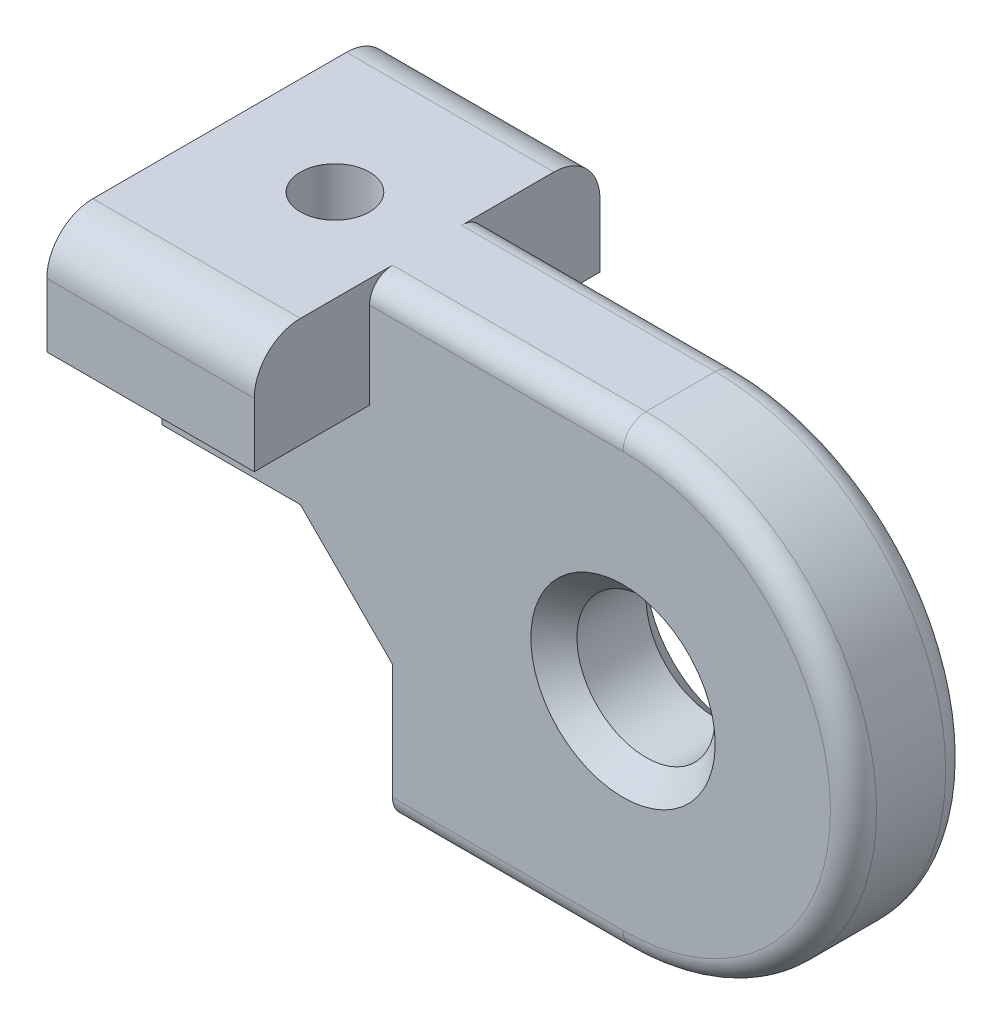
SolidWorks part; units mm, degrees
ref_plane "Front Plane" through (0, 0, 0) normal (0, 0, 1) x (1, 0, 0)
ref_plane "Top Plane" through (0, 0, 0) normal (0, 1, 0) x (1, 0, 0)
ref_plane "Right Plane" through (0, 0, 0) normal (1, 0, 0) x (0, 0, -1)
sketch "Sketch1" plane through (0, 0, 0) normal (0, 0, 1) x (1, 0, 0)
  line L0 (0, 10) -> (-20, 10)
  line L1 (-20, 10) -> (-20, 0)
  line L2 (-10, -10) -> (0, -10)
  line L3 (-20, 0) -> (-14, 0)
  line L4 (55, 0) -> (-55, 0) construction
  line L5 (-10, -4) -> (-10, -10)
  line L6 (-14, 0) -> (-10, -4)
  arc A0 (0, -10) -> (0, 10) centre (0, 0) ccw
  circle A1 centre (0, 0) radius 3
  point P6 (-10, 0)
  dimension "D1" = 20
  dimension "D2" = 6
  dimension "D3" = 20
  dimension "D4" = 10
extrude "Boss-Extrude1" add sketch "Sketch1" along normal mid plane 5
sketch "Sketch2" plane through (0, 0, 0) normal (0, 0, 1) x (1, 0, 0)
  line L0 (-20, 10) -> (-20, 5.2381)
  line L1 (-11, 5.2381) -> (-11, 10)
  line L2 (-11, 10) -> (-20, 10)
  line L5 (-20, 5.2381) -> (-11, 5.2381)
  dimension "D1" = 9
  dimension "D2" = 4.7619
extrude "Boss-Extrude2" add sketch "Sketch2" along normal mid plane 15
fillet "Fillet1" radius 2 2 edges at (-15.5, 10, -7.5) (-15.5, 10, 7.5)
chamfer "Chamfer1" distance 1 angle 45 2 edges at (3, 0, -2.5) (3, 0, 2.5)
fillet "Fillet2" radius 1 6 edges at (-5, -10, -2.5) (-5.5, 10, -2.5) (-5, -10, 2.5) (-5.5, 10, 2.5) (10, 0, -2.5) (10, 0, 2.5)
sketch "Sketch3" plane through (0, 10, 0) normal (0, 1, 0) x (1, 0, 0)
  line L0 (-11, 0) -> (11, 0) construction
  line L1 (-20, -5.5) -> (-20, 5.5) construction
  circle A0 centre (-15, 0) radius 1.5
  dimension "D1" = 3
  dimension "D2" = 5
extrude "Cut-Extrude1" cut sketch "Sketch3" against normal blind 20
